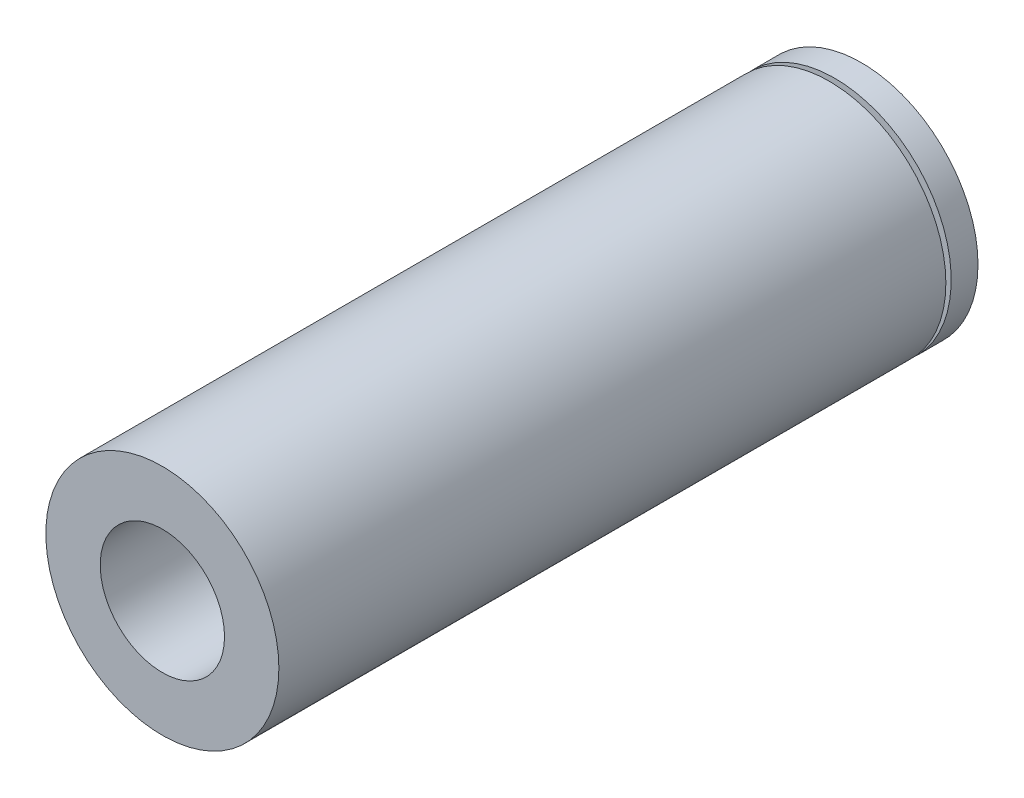
SolidWorks part; units mm, degrees
ref_plane "前视基准面" through (0, 0, 0) normal (0, 0, 1) x (1, 0, 0)
ref_plane "上视基准面" through (0, 0, 0) normal (0, 1, 0) x (1, 0, 0)
ref_plane "右视基准面" through (0, 0, 0) normal (1, 0, 0) x (0, 0, -1)
sketch "草图1" plane through (0, 0, 0) normal (0, 0, 1) x (1, 0, 0)
  circle A0 centre (0, 0) radius 4
  circle A1 centre (0, 0) radius 7.5
  dimension "D1" = 8
  dimension "D2" = 15
extrude "凸台-拉伸1" add sketch "草图1" along normal blind 45
sketch "草图2" plane through (0, 0, 0) normal (0, 1, 0) x (1, 0, 0)
  line L0 (7.5, -45) -> (7.5, 0) construction
  line L1 (6.9859, -1.7256) -> (8.0141, -1.7256)
  line L2 (6.9859, -1.7256) -> (6.9859, -2.068)
  line L3 (6.9859, -2.068) -> (8.0141, -2.068)
  line L4 (8.0141, -1.7256) -> (8.0141, -2.068)
  line L14 (7.5, -43.27) -> (8.53, -43.27)
  line L15 (8.53, -43.27) -> (8.53, -42.93)
  line L16 (8.53, -42.93) -> (7.5, -42.93)
  line L17 (7.5, -42.93) -> (7.5, -43.27)
  point P0 (7.5, -1.8968)
ref_axis "基准轴1" through (0, 0, 0) along (0, 0, -1)
revolve "切除-旋转1" cut sketch "草图2" angle 360 about axis through (0, 0, 0) along (0, 0, -1)
